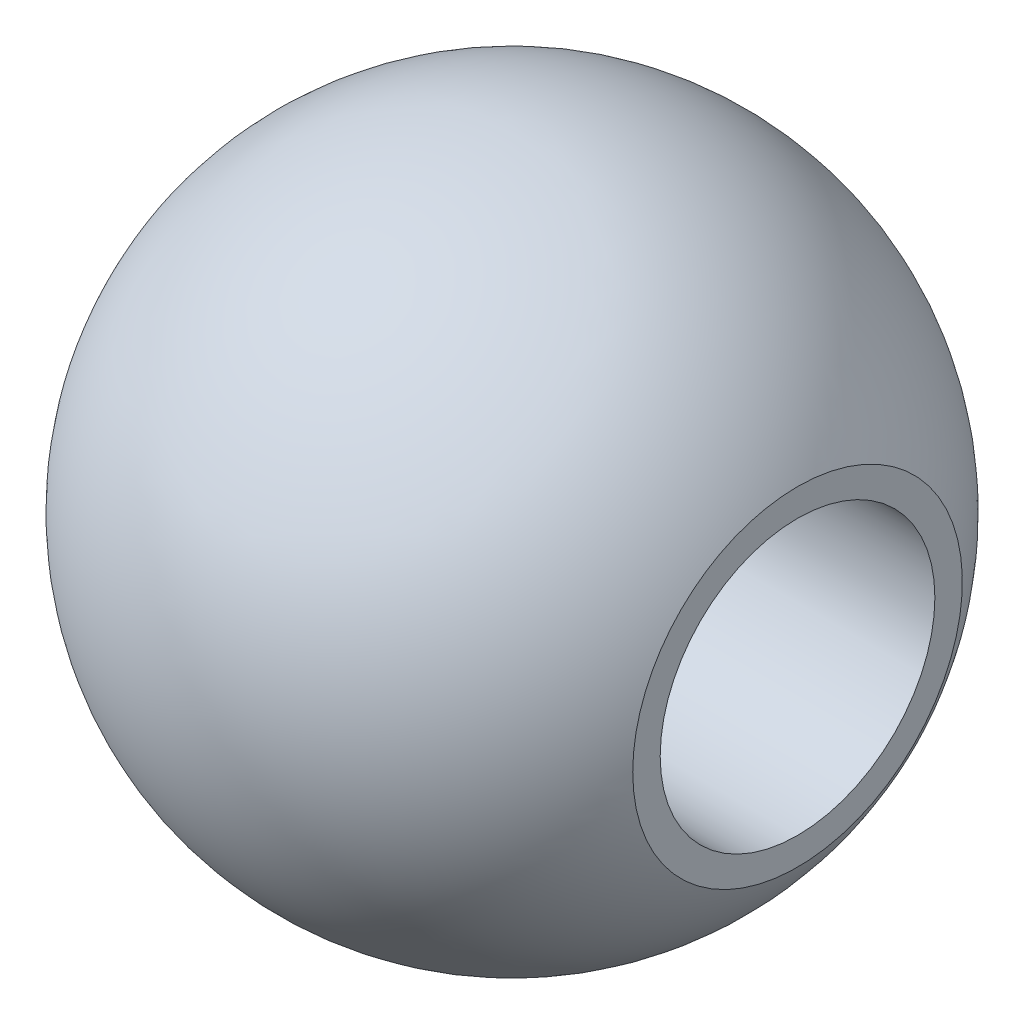
SolidWorks part; units mm, degrees
ref_plane "Front Plane" through (0, 0, 0) normal (0, 0, 1) x (1, 0, 0)
ref_plane "Top Plane" through (0, 0, 0) normal (0, 1, 0) x (1, 0, 0)
ref_plane "Right Plane" through (0, 0, 0) normal (1, 0, 0) x (0, 0, -1)
sketch "Sketch1" plane through (0, 0, 0) normal (0, 0, 1) x (1, 0, 0)
  line L0 (-3.5, 0) -> (3.5, 0) construction
  line L1 (-3.5, 0) -> (-3.5, 2) construction
  line L2 (-3.5, 2) -> (-2.2361, 2) construction
  line L3 (0, 0) -> (0, 4) construction
  line L4 (3.5, 0) -> (3.5, 2) construction
  line L5 (3.5, 2) -> (2.2361, 2) construction
  line L6 (-3, 0) -> (2.5981, 0)
  line L7 (2.5981, 1.5) -> (2.5981, 0)
  arc A0 (2.5981, 1.5) -> (-3, 0) centre (0, 0) ccw
  dimension "D3" = 3
  dimension "D1" = 3.5
  dimension "D2" = 2
  dimension "D4" = 3
revolve "Revolve1" add sketch "Sketch1" angle 360 about L0
ref_point "Point1"
ref_plane "Plane1" through (3, 0, 0) normal (1, 0, 0) x (0, 0, -1)
hole_wizard "Tap Drill for M3x0.5 Tap1" positions "Sketch4" profile "Sketch3" hole size "M3x0.5" standard "ANSI Metric"
sketch "Sketch4" plane through (3, 0, 0) normal (1, 0, 0) x (0, 0, -1)
  point P0 (0, 0)
sketch "Sketch3" plane through (3, 0, 0) normal (0, 1, 0) x (0, 0, -1)
  line L0 (0, 0) -> (0, 4.7511)
  line L1 (0, 4.7511) -> (1.25, 4)
  line L2 (1.25, 4) -> (1.25, 0)
  line L5 (1.25, 0) -> (0, 0)
  line L10 (0, 4.7511) -> (-1.25, 4) construction
  line L11 (0, -6.35) -> (0, 107.95) construction
  dimension "Hole Dia." = 2.5
  dimension "Hole Depth" = 4
  dimension "Drill Angle" = 118
cosmetic thread "Cosmetic Thread1"
